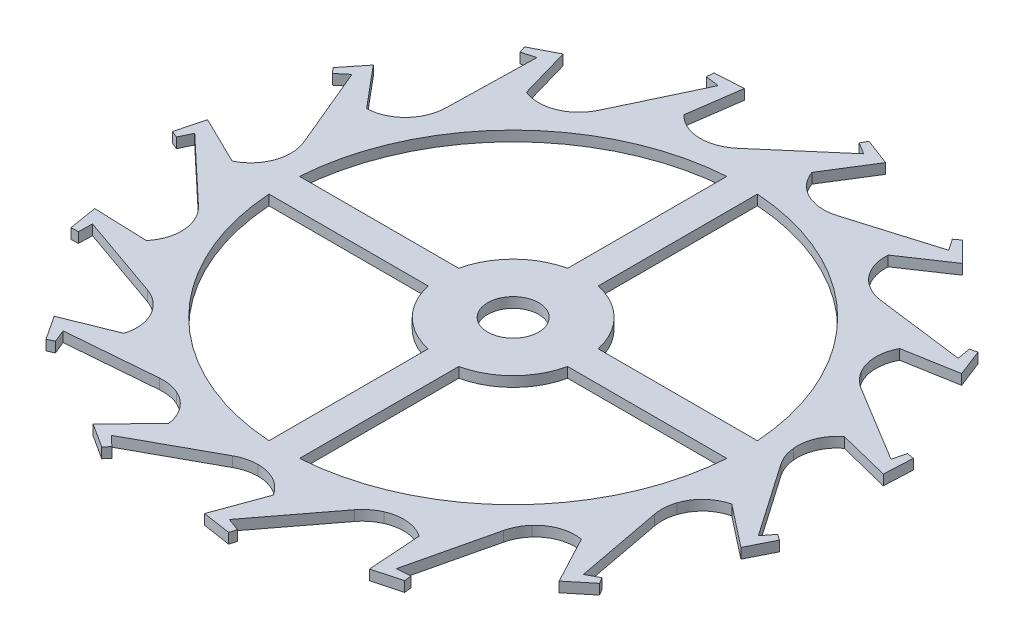
SolidWorks part; units mm, degrees
ref_plane "Alzado" through (0, 0, 0) normal (0, 0, 1) x (1, 0, 0)
ref_plane "Planta" through (0, 0, 0) normal (0, 1, 0) x (1, 0, 0)
ref_plane "Vista lateral" through (0, 0, 0) normal (1, 0, 0) x (0, 0, -1)
sketch "Sketch1" plane through (0, 0, 0) normal (0, 1, 0) x (1, 0, 0)
  line L0 (0, 0) -> (-1.4657, -3.2921) construction
  line L1 (-2.0928, -2.321) -> (-1.2205, -2.2492)
  line L2 (-2.042, -2.4459) -> (-2.0928, -2.321)
  line L3 (-2.1056, -2.4757) -> (-2.042, -2.4459)
  line L4 (-2.26, -2.2404) -> (-2.1056, -2.4757)
  line L5 (-1.7732, -2.0443) -> (-2.26, -2.2404)
  line L6 (-2.8559, -1.2692) -> (-2.0298, -1.5584)
  line L7 (-2.8602, -1.4039) -> (-2.8559, -1.2692)
  line L8 (-2.9305, -1.4053) -> (-2.8602, -1.4039)
  line L9 (-2.9759, -1.1275) -> (-2.9305, -1.4053)
  line L10 (-2.4514, -1.1463) -> (-2.9759, -1.1275)
  line L11 (-3.1252, 0.0022) -> (-2.4882, -0.598)
  line L12 (-3.184, -0.1191) -> (-3.1252, 0.0022)
  line L13 (-3.2487, -0.0918) -> (-3.184, -0.1191)
  line L14 (-3.1772, 0.1804) -> (-3.2487, -0.0918)
  line L15 (-2.7057, -0.0501) -> (-3.1772, 0.1804)
  line L16 (-2.8542, 1.2731) -> (-2.5163, 0.4657)
  line L17 (-2.9572, 1.1862) -> (-2.8542, 1.2731)
  line L18 (-3.0052, 1.2375) -> (-2.9572, 1.1862)
  line L19 (-2.8291, 1.4571) -> (-3.0052, 1.2375)
  line L20 (-2.4922, 1.0547) -> (-2.8291, 1.4571)
  line L21 (-2.0896, 2.324) -> (-2.1093, 1.4489)
  line L22 (-2.219, 2.2864) -> (-2.0896, 2.324)
  line L23 (-2.2421, 2.3528) -> (-2.219, 2.2864)
  line L24 (-1.9919, 2.4818) -> (-2.2421, 2.3528)
  line L25 (-1.8477, 1.9772) -> (-1.9919, 2.4818)
  line L26 (-0.9637, 2.9729) -> (-1.3377, 2.1816)
  line L27 (-1.0972, 2.9913) -> (-0.9637, 2.9729)
  line L28 (-1.0913, 3.0613) -> (-1.0972, 2.9913)
  line L29 (-0.8102, 3.0774) -> (-1.0913, 3.0613)
  line L30 (-0.8838, 2.5578) -> (-0.8102, 3.0774)
  line L31 (0.3288, 3.1079) -> (-0.3347, 2.5371)
  line L32 (0.2143, 3.179) -> (0.3288, 3.1079)
  line L33 (0.2482, 3.2405) -> (0.2143, 3.179)
  line L34 (0.5115, 3.1409) -> (0.2482, 3.2405)
  line L35 (0.233, 2.6962) -> (0.5115, 3.1409)
  line L36 (1.5645, 2.7054) -> (0.7262, 2.4538)
  line L37 (1.4888, 2.817) -> (1.5645, 2.7054)
  line L38 (1.5448, 2.8594) -> (1.4888, 2.817)
  line L39 (1.7448, 2.6613) -> (1.5448, 2.8594)
  line L40 (-0.7885, -2.5888) -> (-1.1534, -2.966)
  line L41 (-1.1534, -2.966) -> (-0.9166, -3.1181)
  line L42 (-0.9166, -3.1181) -> (-0.8706, -3.065)
  line L43 (-0.8706, -3.065) -> (-0.9678, -2.9716)
  line L44 (-0.9678, -2.9716) -> (-0.2001, -2.5512)
  line L45 (1.3095, 2.3683) -> (1.7448, 2.6613)
  line L46 (2.5296, 1.8352) -> (1.6615, 1.9463)
  line L47 (2.5059, 1.9679) -> (2.5296, 1.8352)
  line L48 (2.5743, 1.9838) -> (2.5059, 1.9679)
  line L49 (2.6764, 1.7216) -> (2.5743, 1.9838)
  line L50 (2.1595, 1.6309) -> (2.6764, 1.7216)
  line L51 (3.0574, 0.6476) -> (2.3095, 1.1023)
  line L52 (3.0896, 0.7785) -> (3.0574, 0.6476)
  line L53 (3.1586, 0.7653) -> (3.0896, 0.7785)
  line L54 (3.1453, 0.4841) -> (3.1586, 0.7653)
  line L55 (2.6362, 0.6116) -> (3.1453, 0.4841)
  line L56 (3.0565, -0.6519) -> (2.5582, 0.0676)
  line L57 (3.1392, -0.5454) -> (3.0565, -0.6519)
  line L58 (3.1968, -0.5856) -> (3.1392, -0.5454)
  line L59 (3.0703, -0.837) -> (3.1968, -0.5856)
  line L60 (2.657, -0.5135) -> (3.0703, -0.837)
  line L61 (2.5271, -1.8387) -> (2.3645, -0.9787)
  line L62 (2.6459, -1.7751) -> (2.5271, -1.8387)
  line L63 (2.6822, -1.8352) -> (2.6459, -1.7751)
  line L64 (2.4644, -2.0135) -> (2.6822, -1.8352)
  line L65 (2.2184, -1.5498) -> (2.4644, -2.0135)
  line L66 (1.5607, -2.7076) -> (1.762, -1.8558)
  line L67 (1.6952, -2.6978) -> (1.5607, -2.7076)
  line L68 (1.7039, -2.7675) -> (1.6952, -2.6978)
  line L69 (1.4324, -2.8417) -> (1.7039, -2.7675)
  line L70 (1.3963, -2.3182) -> (1.4324, -2.8417)
  line L71 (0.3245, -3.1083) -> (0.8548, -2.412)
  line L72 (0.4513, -3.1541) -> (0.3245, -3.1083)
  line L73 (0.4309, -3.2213) -> (0.4513, -3.1541)
  line L74 (0.1527, -3.1787) -> (0.4309, -3.2213)
  line L75 (0, -1000) -> (0, 49000) construction
  line L76 (-1000, 0) -> (49000, 0) construction
  line L77 (0.3327, -2.6857) -> (0.1527, -3.1787)
  circle A0 centre (0, 0) radius 2.5 construction
  circle A1 centre (0, 0) radius 2.8908 construction
  circle A2 centre (0, 0) radius 2.9167 construction
  circle A3 centre (0, 0) radius 3.1252 construction
  circle A4 centre (0, 0) radius 3.1823 construction
  circle A5 centre (0, 0) radius 3.25 construction
  circle A6 centre (0, 0) radius 2.7062 construction
  arc A7 (-1.2205, -2.2492) -> (-1.0168, -2.2839) centre (-1.1863, -2.6645) cw
  arc A8 (-1.8579, -1.6728) -> (-1.7732, -2.0443) centre (-2.1483, -1.9344) cw
  arc A9 (-2.0298, -1.5584) -> (-1.8579, -1.6728) centre (-2.1675, -1.9516) cw
  arc A10 (-2.3776, -0.7725) -> (-2.4514, -1.1463) centre (-2.7494, -0.8933) cw
  arc A11 (-2.4882, -0.598) -> (-2.3776, -0.7725) centre (-2.7739, -0.9013) cw
  arc A12 (-2.4863, 0.2613) -> (-2.7057, -0.0501) centre (-2.875, 0.3022) cw
  arc A13 (-2.5163, 0.4657) -> (-2.4863, 0.2613) centre (-2.9007, 0.3049) cw
  arc A14 (-2.1651, 1.25) -> (-2.4922, 1.0547) centre (-2.5035, 1.4454) cw
  arc A15 (-2.1093, 1.4489) -> (-2.1651, 1.25) centre (-2.5259, 1.4583) cw
  arc A16 (-1.4695, 2.0225) -> (-1.8477, 1.9772) centre (-1.6992, 2.3387) cw
  arc A17 (-1.0168, -2.2839) -> (-0.7885, -2.5888) centre (-1.1758, -2.6409) cw
  arc A18 (-0.2001, -2.5512) -> (0, -2.5) centre (0, -2.9167) cw
  arc A19 (-1.3377, 2.1816) -> (-1.4695, 2.0225) centre (-1.7144, 2.3596) cw
  arc A20 (-0.5198, 2.4454) -> (-0.8838, 2.5578) centre (-0.601, 2.8277) cw
  arc A21 (-0.3347, 2.5371) -> (-0.5198, 2.4454) centre (-0.6064, 2.8529) cw
  arc A22 (0.5198, 2.4454) -> (0.233, 2.6962) centre (0.601, 2.8277) cw
  arc A23 (0.7262, 2.4538) -> (0.5198, 2.4454) centre (0.6064, 2.8529) cw
  arc A24 (1.4695, 2.0225) -> (1.3095, 2.3683) centre (1.6992, 2.3387) cw
  arc A25 (1.6615, 1.9463) -> (1.4695, 2.0225) centre (1.7144, 2.3596) cw
  arc A26 (2.1651, 1.25) -> (2.1595, 1.6309) centre (2.5035, 1.4454) cw
  arc A27 (2.3095, 1.1023) -> (2.1651, 1.25) centre (2.5259, 1.4583) cw
  arc A28 (2.4863, 0.2613) -> (2.6362, 0.6116) centre (2.875, 0.3022) cw
  arc A29 (2.5582, 0.0676) -> (2.4863, 0.2613) centre (2.9007, 0.3049) cw
  arc A30 (2.3776, -0.7725) -> (2.657, -0.5135) centre (2.7494, -0.8933) cw
  arc A31 (2.3645, -0.9787) -> (2.3776, -0.7725) centre (2.7739, -0.9013) cw
  arc A32 (1.8579, -1.6728) -> (2.2184, -1.5498) centre (2.1483, -1.9344) cw
  arc A33 (1.762, -1.8558) -> (1.8579, -1.6728) centre (2.1675, -1.9516) cw
  arc A34 (1.0168, -2.2839) -> (1.3963, -2.3182) centre (1.1758, -2.6409) cw
  arc A35 (0.8548, -2.412) -> (1.0168, -2.2839) centre (1.1863, -2.6645) cw
  arc A36 (0, -2.5) -> (0.3327, -2.6857) centre (0, -2.8908) cw
  point P167 (0, 0)
  dimension "D1" = 24
  dimension "D2" = 0.4167
  dimension "D3" = 0.3908
  dimension "D4" = 5
  dimension "D5" = 5.7817
  dimension "D6" = 5.8334
  dimension "D7" = 6.2505
  dimension "D8" = 6.3646
  dimension "D9" = 6.5
  dimension "D10" = 32.716
  dimension "D11" = 43.834
  dimension "D12" = 28.705
  dimension "D13" = 45.946
  dimension "D14" = 5.4124
  dimension "D15" = 98.149
  dimension "D16" = 15
extrude "Boss-Extrude1" add sketch "Sketch1" along normal blind 0.1
sketch "Sketch2" plane through (0, 0, 0) normal (0, 1, 0) x (1, 0, 0)
  line L0 (0, -1000) -> (0, 49000) construction
  line L1 (0.15, -999.8828) -> (0.15, 49000.1172) construction
  line L2 (-0.15, -999.7571) -> (-0.15, 49000.2429) construction
  line L3 (-1000, 0) -> (49000, 0) construction
  line L4 (-999.8815, 0.15) -> (49000.1185, 0.15) construction
  line L5 (-1000, -0.15) -> (49000, -0.15) construction
  line L6 (0.15, 2.245) -> (0.15, 0.6837)
  line L7 (0.6837, 0.15) -> (2.245, 0.15)
  line L8 (-0.15, -2.245) -> (-0.15, -0.6837)
  line L9 (-2.245, 0.15) -> (-0.6837, 0.15)
  line L10 (0.15, -0.6837) -> (0.15, -2.245)
  line L11 (2.245, -0.15) -> (0.6837, -0.15)
  line L12 (-0.6837, -0.15) -> (-2.245, -0.15)
  line L13 (-0.15, 0.6837) -> (-0.15, 2.245)
  arc A0 (-0.15, 2.245) -> (-2.245, 0.15) centre (0, 0) ccw
  arc A1 (-0.6837, -0.15) -> (-0.15, -0.6837) centre (0, 0) ccw
  arc A2 (-2.245, -0.15) -> (-0.15, -2.245) centre (0, 0) ccw
  arc A3 (0.15, -2.245) -> (2.245, -0.15) centre (0, 0) ccw
  arc A4 (2.245, 0.15) -> (0.15, 2.245) centre (0, 0) ccw
  arc A5 (-0.15, 0.6837) -> (-0.6837, 0.15) centre (0, 0) ccw
  arc A6 (0.6837, 0.15) -> (0.15, 0.6837) centre (0, 0) ccw
  arc A7 (0.15, -0.6837) -> (0.6837, -0.15) centre (0, 0) ccw
  circle A8 centre (0, 0) radius 0.25
  dimension "D5" = 4.5
  dimension "D6" = 1.4
  dimension "D7" = 0.5
  dimension "D1" = 0.15
  dimension "D2" = 0.15
  dimension "D3" = 0.15
  dimension "D4" = 0.15
extrude "Cut-Extrude1" cut sketch "Sketch2" along normal up to next
